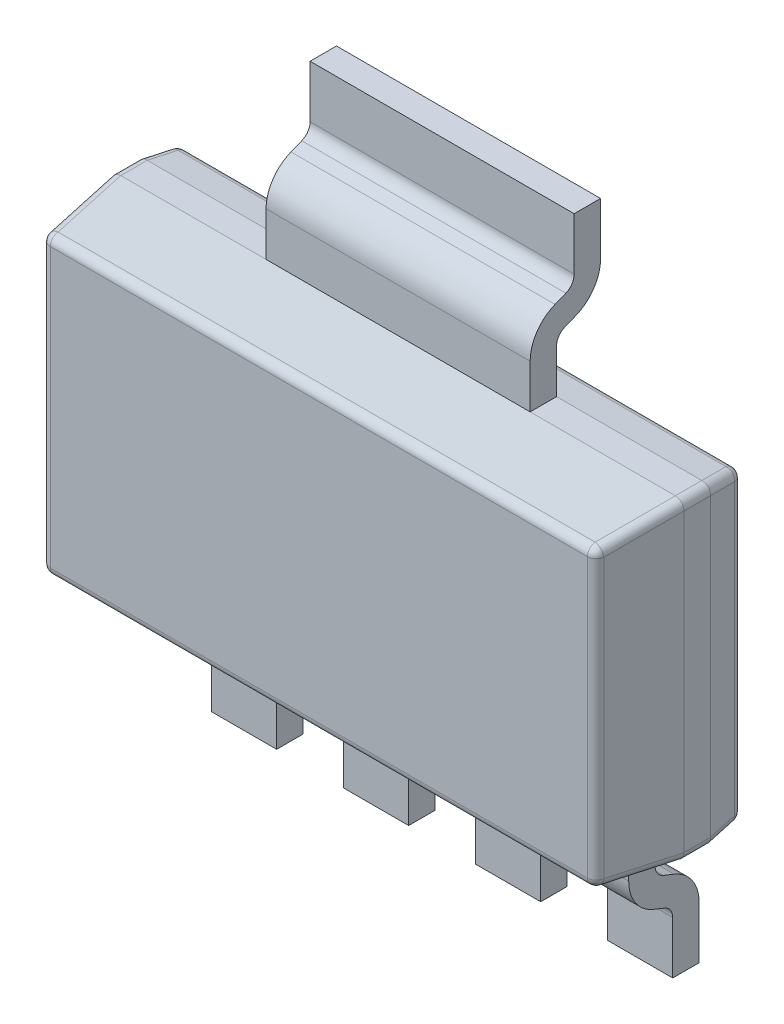
SolidWorks part; units mm, degrees
ref_plane "Front Plane" through (0, 0, 0) normal (0, 0, 1) x (1, 0, 0)
ref_plane "Top Plane" through (0, 0, 0) normal (0, 1, 0) x (1, 0, 0)
ref_plane "Right Plane" through (0, 0, 0) normal (1, 0, 0) x (0, 0, -1)
ref_plane "Plane1" through (0, 0, 0.1) normal (0, 0, 1) x (1, 0, 0)
sketch "Sketch1" plane through (0, 0, 0.1) normal (0, 0, 1) x (1, 0, 0)
  line L1 (-3.25, 1.78) -> (3.25, 1.78)
  line L2 (-3.25, 1.78) -> (-3.25, -1.78)
  line L3 (-3.25, -1.78) -> (3.25, -1.78)
  line L4 (3.25, 1.78) -> (3.25, -1.78)
extrude "Extrude1" add sketch "Sketch1" along normal blind 1.6
chamfer "Chamfer1" distance 0.9 angle 7 4 edges at (0, 1.78, 1.7) (3.25, 0, 1.7) (0, -1.78, 1.7) (-3.25, 0, 1.7)
chamfer "Chamfer2" distance 0.4 angle 7 4 edges at (0, -1.78, 0.1) (3.25, 0, 0.1) (0, 1.78, 0.1) (-3.25, 0, 0.1)
sketch "Sketch2" plane through (0, 0, 0) normal (0, 0, 1) x (1, 0, 0)
  line L0 (-1.12, -3.48) -> (-0.38, -3.48)
  line L2 (3.25, -1.78) -> (-3.25, -1.78) construction
  line L3 (-1.12, -3.48) -> (-1.12, -1.78)
  line L4 (-2.62, -3.48) -> (-1.88, -3.48)
  line L5 (-2.62, -3.48) -> (-2.62, -1.78)
  line L6 (-2.62, -1.78) -> (-1.88, -1.78)
  line L7 (-1.88, -3.48) -> (-1.88, -1.78)
  line L8 (-1.12, -1.78) -> (-0.38, -1.78)
  line L9 (-0.38, -3.48) -> (-0.38, -1.78)
  line L10 (0.38, -3.48) -> (1.12, -3.48)
  line L11 (0.38, -3.48) -> (0.38, -1.78)
  line L12 (0.38, -1.78) -> (1.12, -1.78)
  line L13 (1.12, -3.48) -> (1.12, -1.78)
  line L14 (1.88, -3.48) -> (2.62, -3.48)
  line L15 (1.88, -3.48) -> (1.88, -1.78)
  line L16 (1.88, -1.78) -> (2.62, -1.78)
  line L17 (2.62, -3.48) -> (2.62, -1.78)
  line L18 (-3.25, 1.78) -> (3.25, 1.78) construction
  line L19 (-1.5, 1.78) -> (1.5, 1.78)
  line L20 (-1.5, 1.78) -> (-1.5, 3.48)
  line L21 (-1.5, 3.48) -> (1.5, 3.48)
  line L22 (1.5, 1.78) -> (1.5, 3.48)
extrude "Extrude2" add sketch "Sketch2" along normal blind 0.8
sketch "Sketch3" plane through (2.62, 0, 0) normal (1, 0, 0) x (0, 0, -1)
  line L0 (-0.5, -1.78) -> (-0.5, -2.2784)
  line L1 (-0.4057, -2.4177) -> (-0.2829, -2.4669)
  line L3 (-0.5, -1.78) -> (0, -1.78)
  line L4 (0, -1.78) -> (0, -2.8847)
  line L5 (-0.5171, -2.6963) -> (-0.3943, -2.7454)
  line L6 (-0.3, -3.48) -> (-0.3, -2.8847)
  line L7 (-0.3, -3.48) -> (-0.3, -2.7831) construction
  line L8 (-0.5171, -2.6963) -> (-0.3, -2.7831) construction
  line L9 (-0.4057, -2.4177) -> (0, -2.58) construction
  line L10 (0, -3.48) -> (0, -2.58) construction
  line L11 (-0.8, -1.78) -> (-0.8, -2.2784) construction
  line L12 (-0.8, -2.2784) -> (-0.8, -3.48)
  line L13 (-0.8, -3.48) -> (-0.3, -3.48)
  arc A0 (-0.5, -2.2784) -> (-0.4057, -2.4177) centre (-0.35, -2.2784) ccw
  arc A1 (-0.8, -2.2784) -> (-0.5171, -2.6963) centre (-0.35, -2.2784) ccw
  arc A2 (-0.3, -2.8847) -> (-0.3943, -2.7454) centre (-0.45, -2.8847) ccw
  arc A3 (0, -2.8847) -> (-0.2829, -2.4669) centre (-0.45, -2.8847) ccw
  line B0 (-0.5, 1.78) -> (-0.5, 2.2784)
  line B1 (-0.4057, 2.4177) -> (-0.2829, 2.4669)
  line B2 (-0.3, 3.48) -> (-0.8, 3.48)
  line B3 (-0.8, 3.48) -> (-0.8, 2.2784)
  line B4 (-0.5171, 2.6963) -> (-0.3943, 2.7454)
  line B5 (-0.3, 3.48) -> (-0.3, 2.8847)
  line B6 (0, 2.8847) -> (0, 1.78)
  line B7 (0, 1.78) -> (-0.5, 1.78)
  arc B8 (-0.5, 2.2784) -> (-0.4057, 2.4177) centre (-0.35, 2.2784) cw
  arc B9 (-0.8, 2.2784) -> (-0.5171, 2.6963) centre (-0.35, 2.2784) cw
  arc B10 (-0.3, 2.8847) -> (-0.3943, 2.7454) centre (-0.45, 2.8847) cw
  arc B11 (0, 2.8847) -> (-0.2829, 2.4669) centre (-0.45, 2.8847) cw
sketch_block_instance "Block1-1"
sketch_block "Block1"
extrude "Extrude3" cut sketch "Sketch3" against normal through all
fillet "Fillet1" radius 0.1 20 edges at (0, 1.7309, 0.1) (-3.2009, 0, 0.1) (0, -1.7309, 0.1) (3.2009, 0, 0.1) (0, -1.6695, 1.7) (-3.1395, 0, 1.7) (0, 1.6695, 1.7) (3.1395, 0, 1.7) (3.2254, 1.7554, 0.3) (3.25, 1.78, 0.65) (3.1947, 1.7247, 1.25) (3.2254, -1.7554, 0.3) (3.25, -1.78, 0.65) (3.1947, -1.7247, 1.25) (-3.1947, 1.7247, 1.25) (-3.25, 1.78, 0.65) (-3.2254, 1.7554, 0.3) (-3.2254, -1.7554, 0.3) (-3.25, -1.78, 0.65) (-3.1947, -1.7247, 1.25)
